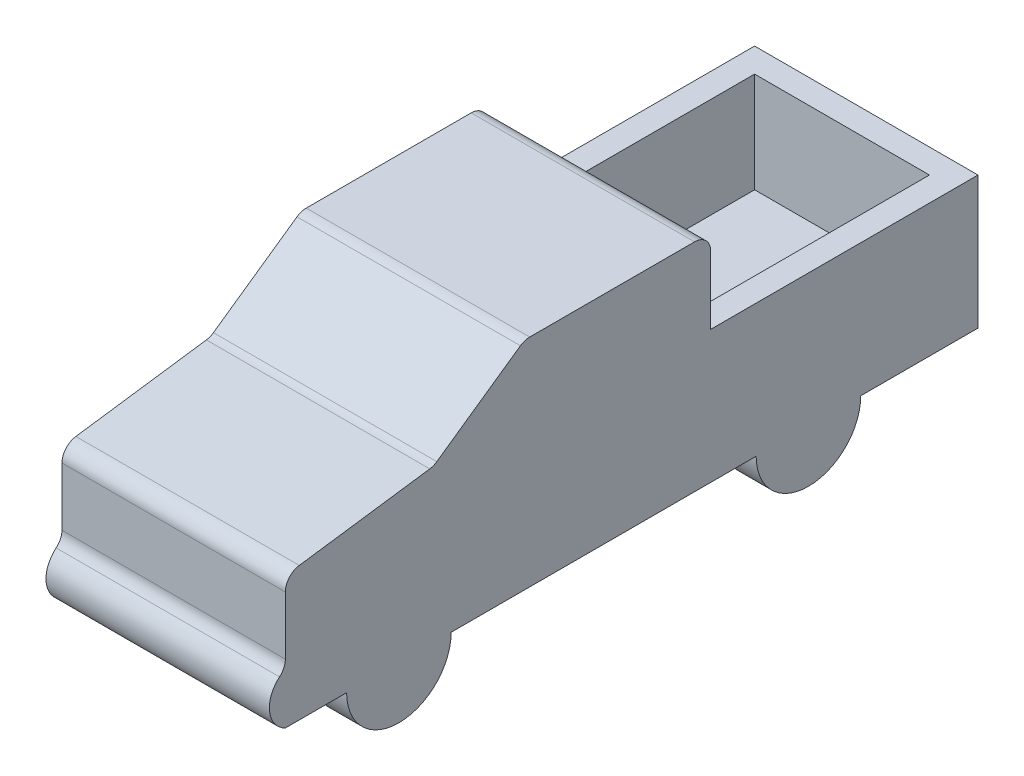
SolidWorks part; units mm, degrees
ref_plane "Front Plane" through (0, 0, 0) normal (0, 0, 1) x (1, 0, 0)
ref_plane "Top Plane" through (0, 0, 0) normal (0, 1, 0) x (1, 0, 0)
ref_plane "Right Plane" through (0, 0, 0) normal (1, 0, 0) x (0, 0, -1)
sketch "Sketch2" plane through (0, 0, 0) normal (1, 0, 0) x (0, 0, -1)
  line L3 (-262.7936, 0) -> (0, 0)
  line L4 (0, 0) -> (165.1, 0)
  line L6 (165.1, 0) -> (165.1, 81.9)
  line L7 (165.1, 81.9) -> (150.1, 81.9)
  line L8 (150.1, 81.9) -> (150.1, 20)
  line L9 (150.1, 20) -> (0, 20)
  line L10 (0, 20) -> (0, 133.7)
  line L11 (0, 133.7) -> (-115, 133.7)
  line L12 (-115, 133.7) -> (-171.1938, 94.3527)
  line L13 (-171.1938, 94.3527) -> (-262.7936, 81.4791)
  line L18 (-262.7936, 81.4791) -> (-262.7936, 31.4791)
  line L19 (-262.7936, 31.4791) -> (-262.7936, 0) construction
  arc A2 (-262.7936, 31.4791) -> (-262.7936, 0) centre (-255.1441, 15.7396) ccw
  dimension "D12" = 17.5
  dimension "D2" = 113.7
  dimension "D3" = 20
  dimension "D4" = 35
  dimension "D5" = 153
  dimension "D6" = 165.1
  dimension "D7" = 15
  dimension "D8" = 61.9
  dimension "D9" = 92.5
  dimension "D10" = 68.6
  dimension "D11" = 50
  dimension "D13" = 115
extrude "Boss-Extrude1" add sketch "Sketch2" along normal mid plane 138
sketch "Sketch4" plane through (0, 20, 0) normal (0, 1, 0) x (1, 0, 0)
  line L0 (69, 150.1) -> (-69, 150.1) construction
  line L1 (69, 0) -> (54, 0)
  line L2 (69, 0) -> (69, 150.1)
  line L3 (69, 150.1) -> (54, 150.1)
  line L4 (54, 0) -> (54, 150.1)
  dimension "D1" = 15
extrude "Boss-Extrude2" add sketch "Sketch4" along normal up to surface (61.9 mm away) up to face at (0, 81.9, -157.6)
mirror "Mirror1" about plane through (0, 0, 0) normal (1, 0, 0) of "Boss-Extrude2"
sketch "Sketch5" plane through (69, 0, 0) normal (1, 0, 0) x (0, 0, -1)
  line L0 (-262.7936, 0) -> (165.1, 0) construction
  line L1 (-224.9441, 0) -> (-160.3441, 0)
  line L2 (28.0559, 0) -> (92.6559, 0)
  arc A0 (-224.9441, 0) -> (-160.3441, 0) centre (-192.6441, 0) ccw
  arc A1 (28.0559, 0) -> (92.6559, 0) centre (60.3559, 0) ccw
  arc A2 (-262.7936, 31.4791) -> (-262.7936, 0) centre (-255.1441, 15.7396) ccw construction
  point P11 (-272.6441, 15.7396)
  dimension "D3" = 32.3
  dimension "D1" = 333
  dimension "D2" = 80
extrude "Boss-Extrude3" add sketch "Sketch5" against normal blind 20.4
mirror "Mirror2" about plane through (0, 0, 0) normal (1, 0, 0) of "Boss-Extrude3"
fillet "Fillet1" radius 10 5 edges at (0, 133.7, 0) (0, 133.7, 115) (0, 94.3527, 171.1938) (0, 81.4791, 262.7936) (0, 31.4791, 262.7936)
sketch "Sketch6" plane through (0, 0, 0) normal (1, 0, 0) x (0, 0, -1)
  line L0 (-192.6441, 0) -> (-192.6441, -32.3) construction
  line L1 (-2192.6441, -32.3) -> (3807.3559, -32.3)
  line L2 (-2192.6441, -32.3) -> (-2192.6441, 1967.7)
  line L3 (-2192.6441, 1967.7) -> (3807.3559, 1967.7)
  line L4 (3807.3559, -32.3) -> (3807.3559, 1967.7)
  arc A0 (-224.9441, 0) -> (-160.3441, 0) centre (-192.6441, 0) ccw construction
  dimension "D1" = 2000
  dimension "D2" = 6000
  dimension "D3" = 2000
extrude "Boss-Extrude4" [suppressed] add sketch "Sketch6" along normal blind 1000 separate body
sketch "Sketch8" plane through (0, 0, 0) normal (1, 0, 0) x (0, 0, -1)
  line L1 (-392.6441, -32.3) -> (487.3559, -32.3)
  line L2 (-392.6441, -32.3) -> (-392.6441, 407.7)
  line L3 (-392.6441, 407.7) -> (487.3559, 407.7)
  line L4 (487.3559, -32.3) -> (487.3559, 407.7)
  arc A0 (-224.9441, 0) -> (-160.3441, 0) centre (-192.6441, 0) ccw construction
  point P7 (-192.6441, -32.3)
  dimension "D1" = 880
  dimension "D2" = 440
  dimension "D3" = 200
extrude "Boss-Extrude5" [suppressed] add sketch "Sketch8" along normal blind 220 separate body
